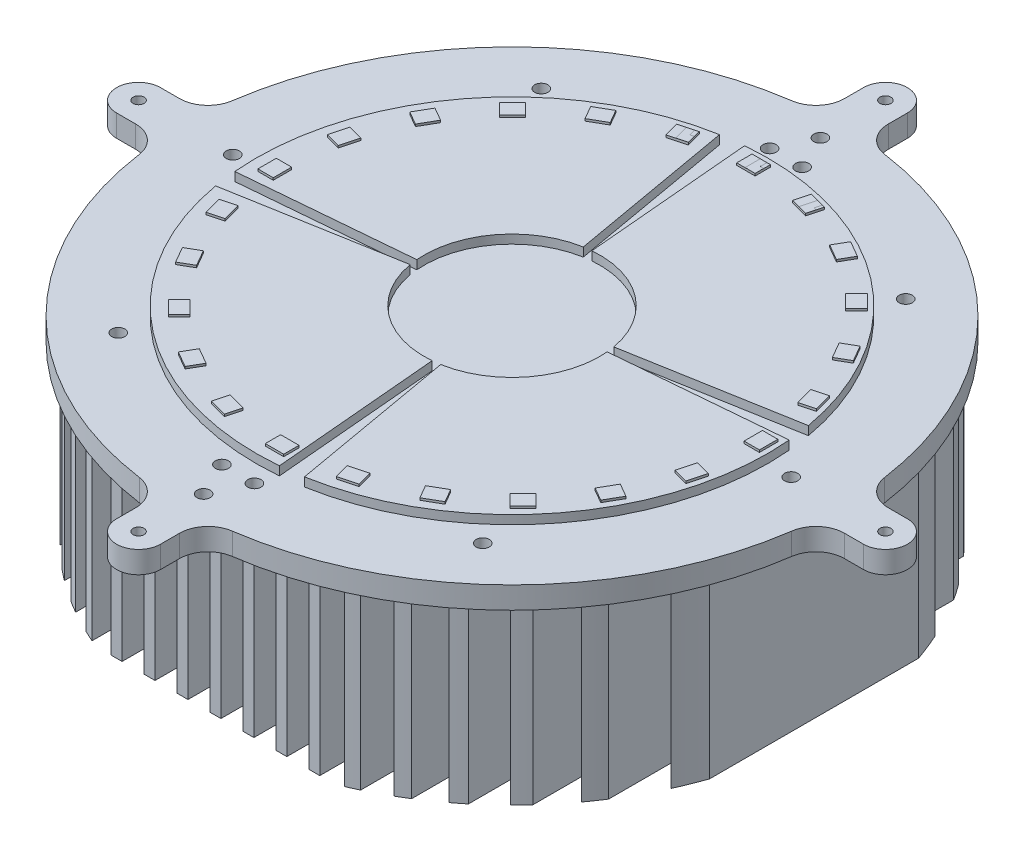
SolidWorks part; units mm, degrees
ref_plane "Front Plane" through (0, 0, 0) normal (0, 0, 1) x (1, 0, 0)
ref_plane "Top Plane" through (0, 0, 0) normal (0, 1, 0) x (1, 0, 0)
ref_plane "Right Plane" through (0, 0, 0) normal (1, 0, 0) x (0, 0, -1)
sketch "Sketch3" plane through (0, 0, 0) normal (0, 1, 0) x (1, 0, 0)
  line L0 (0, 0) -> (211.9111, 0) construction
  line L1 (0, 0) -> (-205.2426, 0) construction
  line L2 (0, 0) -> (0, 170) construction
  line L3 (0, 0) -> (0, -200) construction
  line L4 (161.3691, 10) -> (170, 10)
  line L5 (161.3691, -10) -> (170, -10)
  line L6 (-10, 161.3691) -> (-10, 170)
  line L7 (10, 161.3691) -> (10, 170)
  line L8 (10, -161.3691) -> (10, -170)
  line L9 (-10, -161.3691) -> (-10, -170)
  line L10 (-161.3691, -10) -> (-170, -10)
  line L11 (-161.3691, 10) -> (-170, 10)
  arc A0 (-21.1656, 148.4992) -> (-148.4992, 21.1656) centre (0, 0) ccw
  circle A1 centre (0, 170) radius 2.5
  arc A2 (-10, 170) -> (10, 170) centre (0, 170) cw
  arc A3 (10, 161.3691) -> (21.1656, 148.4992) centre (23, 161.3691) ccw
  arc A4 (-10, 161.3691) -> (-21.1656, 148.4992) centre (-23, 161.3691) cw
  arc A5 (170, 10) -> (170, -10) centre (170, 0) cw
  arc A6 (161.3691, 10) -> (148.4992, 21.1656) centre (161.3691, 23) cw
  circle A7 centre (170, 0) radius 2.5
  arc A8 (161.3691, -10) -> (148.4992, -21.1656) centre (161.3691, -23) ccw
  arc A9 (10, -170) -> (-10, -170) centre (0, -170) cw
  arc A10 (10, -161.3691) -> (21.1656, -148.4992) centre (23, -161.3691) cw
  circle A11 centre (0, -170) radius 2.5
  arc A12 (-10, -161.3691) -> (-21.1656, -148.4992) centre (-23, -161.3691) ccw
  arc A13 (-170, -10) -> (-170, 10) centre (-170, 0) cw
  arc A14 (-161.3691, -10) -> (-148.4992, -21.1656) centre (-161.3691, -23) cw
  circle A15 centre (-170, 0) radius 2.5
  arc A16 (-161.3691, 10) -> (-148.4992, 21.1656) centre (-161.3691, 23) ccw
  arc A17 (-148.4992, -21.1656) -> (-21.1656, -148.4992) centre (0, 0) ccw
  arc A18 (148.4992, 21.1656) -> (21.1656, 148.4992) centre (0, 0) ccw
  arc A19 (21.1656, -148.4992) -> (148.4992, -21.1656) centre (0, 0) ccw
  point P53 (0, 0)
  dimension "D1" = 300
  dimension "D4" = 5
  dimension "D2" = 4
extrude "Boss-Extrude4" add sketch "Sketch3" against normal blind 10
sketch "Sketch4" plane through (0, -10, 0) normal (0, -1, 0) x (1, 0, 0)
  line L0 (0, 0) -> (0, -192.7937) construction
  line L1 (0, 0) -> (0, 216.5128) construction
  line L2 (0, 0) -> (-235.9747, 0) construction
  line L3 (0, 0) -> (242.3846, 0) construction
  line L4 (2.5, -135) -> (-2.5, -135)
  line L5 (2.5, 135) -> (-2.5, 135)
  line L6 (-2.5, -135) -> (-2.5, 135)
  line L7 (2.5, -135) -> (2.5, 135)
  line L8 (12.5, -135) -> (12.5, 135)
  line L9 (17.5, -135) -> (12.5, -135)
  line L10 (17.5, -135) -> (17.5, 135)
  line L11 (17.5, 135) -> (12.5, 135)
  line L12 (27.5, -135) -> (27.5, 135)
  line L13 (32.5, -135) -> (27.5, -135)
  line L14 (32.5, -135) -> (32.5, 135)
  line L15 (32.5, 135) -> (27.5, 135)
  line L16 (42.5, -135) -> (42.5, 135)
  line L17 (47.5, -135) -> (42.5, -135)
  line L18 (47.5, -135) -> (47.5, 135)
  line L19 (47.5, 135) -> (42.5, 135)
  line L20 (57.5, -133.6563) -> (57.5, 133.6563)
  line L22 (62.5, -131.3925) -> (62.5, 131.3925)
  line L24 (72.5, -126.1507) -> (72.5, 126.1507)
  line L26 (77.5, -123.1422) -> (77.5, 123.1422)
  line L28 (87.5, -116.2497) -> (87.5, 116.2497)
  line L30 (92.5, -112.3121) -> (92.5, 112.3121)
  line L32 (102.5, -103.2666) -> (102.5, 103.2666)
  line L34 (107.5, -98.051) -> (107.5, 98.051)
  line L36 (117.5, -85.8138) -> (117.5, 85.8138)
  line L38 (122.5, -78.5111) -> (122.5, 78.5111)
  line L40 (132.5, -60.1166) -> (132.5, 60.1166)
  line L42 (137.5, -47.5815) -> (137.5, 47.5815)
  line L44 (-12.5, -135) -> (-17.5, -135)
  line L45 (-12.5, -135) -> (-12.5, 135)
  line L46 (-17.5, -135) -> (-17.5, 135)
  line L47 (-12.5, 135) -> (-17.5, 135)
  line L48 (-27.5, -135) -> (-32.5, -135)
  line L49 (-27.5, -135) -> (-27.5, 135)
  line L50 (-32.5, -135) -> (-32.5, 135)
  line L51 (-27.5, 135) -> (-32.5, 135)
  line L52 (-42.5, -135) -> (-47.5, -135)
  line L53 (-42.5, -135) -> (-42.5, 135)
  line L54 (-47.5, -135) -> (-47.5, 135)
  line L55 (-42.5, 135) -> (-47.5, 135)
  line L57 (-57.5, -133.6563) -> (-57.5, 133.6563)
  line L58 (-62.5, -131.3925) -> (-62.5, 131.3925)
  line L61 (-72.5, -126.1507) -> (-72.5, 126.1507)
  line L62 (-77.5, -123.1422) -> (-77.5, 123.1422)
  line L65 (-87.5, -116.2497) -> (-87.5, 116.2497)
  line L66 (-92.5, -112.3121) -> (-92.5, 112.3121)
  line L69 (-102.5, -103.2666) -> (-102.5, 103.2666)
  line L70 (-107.5, -98.051) -> (-107.5, 98.051)
  line L73 (-117.5, -85.8138) -> (-117.5, 85.8138)
  line L74 (-122.5, -78.5111) -> (-122.5, 78.5111)
  line L77 (-132.5, -60.1166) -> (-132.5, 60.1166)
  line L78 (-137.5, -47.5815) -> (-137.5, 47.5815)
  line L80 (2.5, -135) -> (-12.5, -135) construction
  line L81 (62.5, 135) -> (57.5, 135) [skipped]
  line L82 (77.5, 135) -> (72.5, 135) [skipped]
  line L83 (92.5, 135) -> (87.5, 135) [skipped]
  line L84 (107.5, 135) -> (102.5, 135) [skipped]
  line L85 (137.5, 135) -> (132.5, 135) [skipped]
  line L86 (122.5, 135) -> (117.5, 135) [skipped]
  line L87 (-57.5, 135) -> (-62.5, 135) [skipped]
  line L88 (-72.5, 135) -> (-77.5, 135) [skipped]
  line L89 (-87.5, 135) -> (-92.5, 135) [skipped]
  line L90 (-102.5, 135) -> (-107.5, 135) [skipped]
  line L91 (-117.5, 135) -> (-122.5, 135) [skipped]
  line L92 (-132.5, 135) -> (-137.5, 135) [skipped]
  line L93 (-57.5, -135) -> (-62.5, -135) [skipped]
  line L94 (62.5, -135) -> (57.5, -135) [skipped]
  line L95 (77.5, -135) -> (72.5, -135) [skipped]
  line L96 (137.5, -135) -> (132.5, -135) [skipped]
  line L97 (122.5, -135) -> (117.5, -135) [skipped]
  line L98 (107.5, -135) -> (102.5, -135) [skipped]
  line L99 (92.5, -135) -> (87.5, -135) [skipped]
  line L100 (-132.5, -135) -> (-137.5, -135) [skipped]
  line L101 (-117.5, -135) -> (-122.5, -135) [skipped]
  line L102 (-102.5, -135) -> (-107.5, -135) [skipped]
  line L103 (-87.5, -135) -> (-92.5, -135) [skipped]
  line L104 (-72.5, -135) -> (-77.5, -135) [skipped]
  arc A2 (132.5, -60.1166) -> (137.5, -47.5815) centre (0, 0) ccw
  arc A3 (117.5, -85.8138) -> (122.5, -78.5111) centre (0, 0) ccw
  arc A4 (102.5, -103.2666) -> (107.5, -98.051) centre (0, 0) ccw
  arc A5 (87.5, -116.2497) -> (92.5, -112.3121) centre (0, 0) ccw
  arc A6 (72.5, -126.1507) -> (77.5, -123.1422) centre (0, 0) ccw
  arc A7 (57.5, -133.6563) -> (62.5, -131.3925) centre (0, 0) ccw
  arc A8 (-77.5, -123.1422) -> (-72.5, -126.1507) centre (0, 0) ccw
  arc A9 (-62.5, -131.3925) -> (-57.5, -133.6563) centre (0, 0) ccw
  arc A10 (-92.5, -112.3121) -> (-87.5, -116.2497) centre (0, 0) ccw
  arc A11 (-107.5, -98.051) -> (-102.5, -103.2666) centre (0, 0) ccw
  arc A12 (-122.5, -78.5111) -> (-117.5, -85.8138) centre (0, 0) ccw
  arc A13 (-137.5, -47.5815) -> (-132.5, -60.1166) centre (0, 0) ccw
  arc A14 (137.5, 47.5815) -> (132.5, 60.1166) centre (0, 0) ccw
  arc A15 (122.5, 78.5111) -> (117.5, 85.8138) centre (0, 0) ccw
  arc A16 (107.5, 98.051) -> (102.5, 103.2666) centre (0, 0) ccw
  arc A17 (92.5, 112.3121) -> (87.5, 116.2497) centre (0, 0) ccw
  arc A18 (77.5, 123.1422) -> (72.5, 126.1507) centre (0, 0) ccw
  arc A19 (62.5, 131.3925) -> (57.5, 133.6563) centre (0, 0) ccw
  arc A20 (-57.5, 133.6563) -> (-62.5, 131.3925) centre (0, 0) ccw
  arc A21 (-72.5, 126.1507) -> (-77.5, 123.1422) centre (0, 0) ccw
  arc A22 (-87.5, 116.2497) -> (-92.5, 112.3121) centre (0, 0) ccw
  arc A23 (-102.5, 103.2666) -> (-107.5, 98.051) centre (0, 0) ccw
  arc A24 (-117.5, 85.8138) -> (-122.5, 78.5111) centre (0, 0) ccw
  arc A25 (-132.5, 60.1166) -> (-137.5, 47.5815) centre (0, 0) ccw
  dimension "D5" = 291
  dimension "D1" = 135
  dimension "D2" = 2.5
  dimension "D4" = 15
  dimension "D3" = 10
extrude "Boss-Extrude5" add sketch "Sketch4" along normal blind 80
sketch "Sketch8" plane through (0, 0, 0) normal (0, 1, 0) x (1, 0, 0)
  line L8 (3.4862, -39.8478) -> (10.1512, -116.0289)
  line L10 (-39.8478, -3.4862) -> (-116.0289, -10.1512)
  line L12 (-3.4862, 39.8478) -> (-10.1512, 116.0289)
  line L14 (39.8478, 3.4862) -> (116.0289, 10.1512)
  line L16 (6.9459, -39.3923) -> (20.2252, -114.7026)
  line L18 (39.3923, 6.9459) -> (114.7026, 20.2252)
  line L20 (-6.9459, 39.3923) -> (-20.2252, 114.7026)
  line L22 (-39.3923, -6.9459) -> (-114.7026, -20.2252)
  line L24 (30.6324, -25.7037) -> (89.1956, -74.844) [skipped]
  line L25 (25.7037, 30.6324) -> (74.844, 89.1956) [skipped]
  line L26 (-30.6324, 25.7037) -> (-89.1956, 74.844) [skipped]
  line L27 (-25.7037, -30.6324) -> (-74.844, -89.1956) [skipped]
  arc A0 (114.7026, 20.2252) -> (-10.1512, 116.0289) centre (0, 0) ccw
  arc A1 (-39.3923, -6.9459) -> (3.4862, -39.8478) centre (0, 0) ccw
  arc A2 (6.9459, -39.3923) -> (39.8478, 3.4862) centre (0, 0) ccw
  arc A3 (39.3923, 6.9459) -> (-3.4862, 39.8478) centre (0, 0) ccw
  arc A9 (-6.9459, 39.3923) -> (-39.8478, -3.4862) centre (0, 0) ccw
  arc A10 (-114.7026, -20.2252) -> (10.1512, -116.0289) centre (0, 0) ccw
  arc A11 (-20.2252, 114.7026) -> (-116.0289, -10.1512) centre (0, 0) ccw
  arc A12 (20.2252, -114.7026) -> (116.0289, 10.1512) centre (0, 0) ccw
  point P15 (0, 0)
  point P22 (0, 0)
  dimension "D2" = 8
extrude "Boss-Extrude7" add sketch "Sketch8" along normal blind 4
sketch "Sketch5" plane through (0, 4, 0) normal (0, 1, 0) x (1, 0, 0)
  line L0 (0, 0) -> (233.0388, 0) construction
  line L1 (0, 0) -> (-266.1331, 0) construction
  line L2 (0, 0) -> (0, 192.8201) construction
  line L3 (0, 0) -> (0, -200.634) construction
  line L4 (0, 113.4586) -> (4.19, 113.4586)
  line L5 (0, 113.4586) -> (-4.19, 113.4586)
  line L6 (4.19, 106.4786) -> (4.19, 113.4586)
  line L7 (-4.19, 106.4786) -> (-4.19, 113.4586)
  line L8 (0, 106.4786) -> (4.19, 106.4786)
  line L9 (0, 106.4786) -> (-4.19, 106.4786)
  line L10 (23.3125, 104.4034) -> (25.119, 111.1456)
  line L11 (29.1663, 110.0611) -> (25.119, 111.1456)
  line L12 (29.1663, 110.0611) -> (33.2135, 108.9767)
  line L13 (31.4069, 102.2345) -> (33.2135, 108.9767)
  line L14 (27.3597, 103.319) -> (31.4069, 102.2345)
  line L15 (27.3597, 103.319) -> (23.3125, 104.4034)
  line L16 (49.3407, 95.2808) -> (52.8307, 101.3256)
  line L17 (56.4594, 99.2306) -> (52.8307, 101.3256)
  line L18 (56.4594, 99.2306) -> (60.088, 97.1356)
  line L19 (56.598, 91.0908) -> (60.088, 97.1356)
  line L20 (52.9694, 93.1858) -> (56.598, 91.0908)
  line L21 (52.9694, 93.1858) -> (49.3407, 95.2808)
  line L22 (72.121, 79.7324) -> (77.0566, 84.668)
  line L23 (80.0194, 81.7052) -> (77.0566, 84.668)
  line L24 (80.0194, 81.7052) -> (82.9821, 78.7425)
  line L25 (78.0465, 73.8068) -> (82.9821, 78.7425)
  line L26 (75.0837, 76.7696) -> (78.0465, 73.8068)
  line L27 (75.0837, 76.7696) -> (72.121, 79.7324)
  line L28 (90.1008, 58.8179) -> (96.1456, 62.3079)
  line L29 (98.2406, 58.6792) -> (96.1456, 62.3079)
  line L30 (98.2406, 58.6792) -> (100.3356, 55.0506)
  line L31 (94.2908, 51.5606) -> (100.3356, 55.0506)
  line L32 (92.1958, 55.1892) -> (94.2908, 51.5606)
  line L33 (92.1958, 55.1892) -> (90.1008, 58.8179)
  line L34 (102.0549, 33.9624) -> (108.797, 35.769)
  line L35 (109.8815, 31.7218) -> (108.797, 35.769)
  line L36 (109.8815, 31.7218) -> (110.9659, 27.6745)
  line L37 (104.2238, 25.868) -> (110.9659, 27.6745)
  line L38 (103.1393, 29.9152) -> (104.2238, 25.868)
  line L39 (103.1393, 29.9152) -> (102.0549, 33.9624)
  line L40 (107.1686, 6.86) -> (114.1486, 6.86)
  line L41 (114.1486, 2.67) -> (114.1486, 6.86)
  line L42 (114.1486, 2.67) -> (114.1486, -1.52)
  line L43 (107.1686, -1.52) -> (114.1486, -1.52)
  line L44 (107.1686, 2.67) -> (107.1686, -1.52)
  line L45 (107.1686, 2.67) -> (107.1686, 6.86)
  line L46 (105.0934, -20.6425) -> (111.8356, -22.449)
  line L47 (110.7511, -26.4963) -> (111.8356, -22.449)
  line L48 (110.7511, -26.4963) -> (109.6667, -30.5435)
  line L49 (102.9245, -28.7369) -> (109.6667, -30.5435)
  line L50 (104.009, -24.6897) -> (102.9245, -28.7369)
  line L51 (104.009, -24.6897) -> (105.0934, -20.6425)
  line L52 (95.9708, -46.6707) -> (102.0156, -50.1607)
  line L53 (99.9206, -53.7894) -> (102.0156, -50.1607)
  line L54 (99.9206, -53.7894) -> (97.8256, -57.418)
  line L55 (91.7808, -53.928) -> (97.8256, -57.418)
  line L56 (93.8758, -50.2994) -> (91.7808, -53.928)
  line L57 (93.8758, -50.2994) -> (95.9708, -46.6707)
  line L58 (80.4224, -69.451) -> (85.358, -74.3866)
  line L59 (82.3952, -77.3494) -> (85.358, -74.3866)
  line L60 (82.3952, -77.3494) -> (79.4325, -80.3121)
  line L61 (74.4968, -75.3765) -> (79.4325, -80.3121)
  line L62 (77.4596, -72.4137) -> (74.4968, -75.3765)
  line L63 (77.4596, -72.4137) -> (80.4224, -69.451)
  line L64 (59.5079, -87.4308) -> (62.9979, -93.4756)
  line L65 (59.3692, -95.5706) -> (62.9979, -93.4756)
  line L66 (59.3692, -95.5706) -> (55.7406, -97.6656)
  line L67 (52.2506, -91.6208) -> (55.7406, -97.6656)
  line L68 (55.8792, -89.5258) -> (52.2506, -91.6208)
  line L69 (55.8792, -89.5258) -> (59.5079, -87.4308)
  line L70 (34.6524, -99.3849) -> (36.459, -106.127)
  line L71 (32.4118, -107.2115) -> (36.459, -106.127)
  line L72 (32.4118, -107.2115) -> (28.3645, -108.2959)
  line L73 (26.558, -101.5538) -> (28.3645, -108.2959)
  line L74 (30.6052, -100.4693) -> (26.558, -101.5538)
  line L75 (30.6052, -100.4693) -> (34.6524, -99.3849)
  line L76 (7.55, -104.4986) -> (7.55, -111.4786)
  line L77 (3.36, -111.4786) -> (7.55, -111.4786)
  line L78 (3.36, -111.4786) -> (-0.83, -111.4786)
  line L79 (-0.83, -104.4986) -> (-0.83, -111.4786)
  line L80 (3.36, -104.4986) -> (-0.83, -104.4986)
  line L81 (3.36, -104.4986) -> (7.55, -104.4986)
  line L82 (-19.9525, -102.4234) -> (-21.759, -109.1656)
  line L83 (-25.8063, -108.0811) -> (-21.759, -109.1656)
  line L84 (-25.8063, -108.0811) -> (-29.8535, -106.9967)
  line L85 (-28.0469, -100.2545) -> (-29.8535, -106.9967)
  line L86 (-23.9997, -101.339) -> (-28.0469, -100.2545)
  line L87 (-23.9997, -101.339) -> (-19.9525, -102.4234)
  line L88 (-45.9807, -93.3008) -> (-49.4707, -99.3456)
  line L89 (-53.0994, -97.2506) -> (-49.4707, -99.3456)
  line L90 (-53.0994, -97.2506) -> (-56.728, -95.1556)
  line L91 (-53.238, -89.1108) -> (-56.728, -95.1556)
  line L92 (-49.6094, -91.2058) -> (-53.238, -89.1108)
  line L93 (-49.6094, -91.2058) -> (-45.9807, -93.3008)
  line L94 (-68.761, -77.7524) -> (-73.6966, -82.688)
  line L95 (-76.6594, -79.7252) -> (-73.6966, -82.688)
  line L96 (-76.6594, -79.7252) -> (-79.6221, -76.7625)
  line L97 (-74.6865, -71.8268) -> (-79.6221, -76.7625)
  line L98 (-71.7237, -74.7896) -> (-74.6865, -71.8268)
  line L99 (-71.7237, -74.7896) -> (-68.761, -77.7524)
  line L100 (-86.7408, -56.8379) -> (-92.7856, -60.3279)
  line L101 (-94.8806, -56.6992) -> (-92.7856, -60.3279)
  line L102 (-94.8806, -56.6992) -> (-96.9756, -53.0706)
  line L103 (-90.9308, -49.5806) -> (-96.9756, -53.0706)
  line L104 (-88.8358, -53.2092) -> (-90.9308, -49.5806)
  line L105 (-88.8358, -53.2092) -> (-86.7408, -56.8379)
  line L106 (-98.6949, -31.9824) -> (-105.437, -33.789)
  line L107 (-106.5215, -29.7418) -> (-105.437, -33.789)
  line L108 (-106.5215, -29.7418) -> (-107.6059, -25.6945)
  line L109 (-100.8638, -23.888) -> (-107.6059, -25.6945)
  line L110 (-99.7793, -27.9352) -> (-100.8638, -23.888)
  line L111 (-99.7793, -27.9352) -> (-98.6949, -31.9824)
  line L112 (-103.8086, -4.88) -> (-110.7886, -4.88)
  line L113 (-110.7886, -0.69) -> (-110.7886, -4.88)
  line L114 (-110.7886, -0.69) -> (-110.7886, 3.5)
  line L115 (-103.8086, 3.5) -> (-110.7886, 3.5)
  line L116 (-103.8086, -0.69) -> (-103.8086, 3.5)
  line L117 (-103.8086, -0.69) -> (-103.8086, -4.88)
  line L118 (-101.7334, 22.6225) -> (-108.4756, 24.429)
  line L119 (-107.3911, 28.4763) -> (-108.4756, 24.429)
  line L120 (-107.3911, 28.4763) -> (-106.3067, 32.5235)
  line L121 (-99.5645, 30.7169) -> (-106.3067, 32.5235)
  line L122 (-100.649, 26.6697) -> (-99.5645, 30.7169)
  line L123 (-100.649, 26.6697) -> (-101.7334, 22.6225)
  line L124 (-92.6108, 48.6507) -> (-98.6556, 52.1407)
  line L125 (-96.5606, 55.7694) -> (-98.6556, 52.1407)
  line L126 (-96.5606, 55.7694) -> (-94.4656, 59.398)
  line L127 (-88.4208, 55.908) -> (-94.4656, 59.398)
  line L128 (-90.5158, 52.2794) -> (-88.4208, 55.908)
  line L129 (-90.5158, 52.2794) -> (-92.6108, 48.6507)
  line L130 (-77.0624, 71.431) -> (-81.998, 76.3666)
  line L131 (-79.0352, 79.3294) -> (-81.998, 76.3666)
  line L132 (-79.0352, 79.3294) -> (-76.0725, 82.2921)
  line L133 (-71.1368, 77.3565) -> (-76.0725, 82.2921)
  line L134 (-74.0996, 74.3937) -> (-71.1368, 77.3565)
  line L135 (-74.0996, 74.3937) -> (-77.0624, 71.431)
  line L136 (-56.1479, 89.4108) -> (-59.6379, 95.4556)
  line L137 (-56.0092, 97.5506) -> (-59.6379, 95.4556)
  line L138 (-56.0092, 97.5506) -> (-52.3806, 99.6456)
  line L139 (-48.8906, 93.6008) -> (-52.3806, 99.6456)
  line L140 (-52.5192, 91.5058) -> (-48.8906, 93.6008)
  line L141 (-52.5192, 91.5058) -> (-56.1479, 89.4108)
  line L142 (-31.2924, 101.3649) -> (-33.099, 108.107)
  line L143 (-29.0518, 109.1915) -> (-33.099, 108.107)
  line L144 (-29.0518, 109.1915) -> (-25.0045, 110.2759)
  line L145 (-23.198, 103.5338) -> (-25.0045, 110.2759)
  line L146 (-27.2452, 102.4493) -> (-23.198, 103.5338)
  line L147 (-27.2452, 102.4493) -> (-31.2924, 101.3649)
  point P33 (1.68, 0.99)
  dimension "D1" = 4.19
  dimension "D2" = 6.98
  dimension "D4" = 4.19
  dimension "D3" = 24
extrude "Boss-Extrude6" add sketch "Sketch5" along normal blind 1
sketch "Sketch7" plane through (0, 0, 0) normal (0, 1, 0) x (1, 0, 0)
  line L0 (0, 0) -> (0, 199.2983) construction
  line L1 (180, 0) -> (-209.1437, 0) construction
  line L2 (0, 0) -> (0, -219.846) construction
  arc A0 (170, -10) -> (170, 10) centre (170, 0) ccw construction
  circle A1 centre (-127.0882, 0) radius 3
  circle A2 centre (0, 140.3779) radius 3
  circle A3 centre (0, -140.3779) radius 3
  circle A4 centre (127.0882, 0) radius 3
  circle A5 centre (-67.7124, 0) radius 3
  circle A6 centre (-52.1309, 49.6625) radius 3
  circle A7 centre (52.1309, 49.6625) radius 3
  circle A8 centre (52.1309, -49.6625) radius 3
  circle A9 centre (-52.1309, -49.6625) radius 3
  circle A10 centre (67.7124, 0) radius 3
  circle A11 centre (-82.9543, 96.2809) radius 3
  circle A12 centre (82.9543, 96.2809) radius 3
  circle A13 centre (82.9543, -96.2809) radius 3
  circle A14 centre (-82.9543, -96.2809) radius 3
  circle A15 centre (7.3999, -124.6624) radius 3
  circle A16 centre (-7.3999, -124.6624) radius 3
  circle A17 centre (7.3999, 124.6624) radius 3
  circle A18 centre (-7.3999, 124.6624) radius 3
  dimension "D2" = 6
extrude "Cut-Extrude1" cut sketch "Sketch7" against normal blind 10
sketch "Sketch10" plane through (0, 5, 0) normal (0, 1, 0) x (1, 0, 0)
  line L0 (-4.19, 113.4586) -> (-4.19, 106.4786)
  line L1 (-4.19, 106.4786) -> (4.19, 106.4786)
  line L2 (4.19, 106.4786) -> (4.19, 113.4586)
  line L3 (4.19, 113.4586) -> (-4.19, 113.4586)
  line L4 (0, 113.4586) -> (0.0001, 113.4586)
  line L5 (2.625, 113.3936) -> (2.625, 110.3936)
  line L6 (4.125, 110.3936) -> (4.125, 106.5436)
  line L7 (4.125, 106.5436) -> (-0.425, 106.5436)
  line L8 (0, 0) -> (0, 207.6989) construction
  line L9 (0, 0) -> (0, -235.1351) construction
  line L10 (2.625, 110.3936) -> (4.125, 110.3936)
  line L11 (-0.425, 113.3936) -> (-0.425, 106.5436)
  line L12 (2.625, 113.3936) -> (-0.425, 113.3936)
  line L13 (0, 0) -> (238.2914, 0) construction
  line L14 (0, 0) -> (-206.0878, 0) construction
  line L15 (31.2113, 106.34) -> (32.3574, 106.0329)
  line L16 (32.3574, 106.0329) -> (31.361, 102.3141)
  line L17 (31.361, 102.3141) -> (27.2688, 103.4106)
  line L18 (29.0417, 110.0272) -> (27.2688, 103.4106)
  line L19 (31.9878, 109.2378) -> (29.0417, 110.0272)
  line L20 (31.9878, 109.2378) -> (31.2113, 106.34)
  line L21 (57.4701, 94.2911) -> (58.7691, 93.5411)
  line L22 (58.7691, 93.5411) -> (56.8441, 90.2069)
  line L23 (56.8441, 90.2069) -> (52.9037, 92.4819)
  line L24 (56.3287, 98.4142) -> (52.9037, 92.4819)
  line L25 (58.9701, 96.8892) -> (56.3287, 98.4142)
  line L26 (58.9701, 96.8892) -> (57.4701, 94.2911)
  line L27 (79.9162, 76.2039) -> (80.9769, 75.1432)
  line L28 (80.9769, 75.1432) -> (78.2545, 72.4209)
  line L29 (78.2545, 72.4209) -> (75.0372, 75.6382)
  line L30 (79.8808, 80.4819) -> (75.0372, 75.6382)
  line L31 (82.0375, 78.3252) -> (79.8808, 80.4819)
  line L32 (82.0375, 78.3252) -> (79.9162, 76.2039)
  line L33 (96.9161, 52.9235) -> (97.6661, 51.6244)
  line L34 (97.6661, 51.6244) -> (94.3319, 49.6994)
  line L35 (94.3319, 49.6994) -> (92.0569, 53.6398)
  line L36 (97.9892, 57.0648) -> (92.0569, 53.6398)
  line L37 (99.5142, 54.4235) -> (97.9892, 57.0648)
  line L38 (99.5142, 54.4235) -> (96.9161, 52.9235)
  line L39 (107.3114, 26.0364) -> (107.6996, 24.5875)
  line L40 (107.6996, 24.5875) -> (103.9808, 23.5911)
  line L41 (103.9808, 23.5911) -> (102.8032, 27.986)
  line L42 (109.4198, 29.7589) -> (102.8032, 27.986)
  line L43 (110.2092, 26.8129) -> (109.4198, 29.7589)
  line L44 (110.2092, 26.8129) -> (107.3114, 26.0364)
  line L45 (110.3936, -2.625) -> (110.3936, -4.125)
  line L46 (110.3936, -4.125) -> (106.5436, -4.125)
  line L47 (106.5436, -4.125) -> (106.5436, 0.425)
  line L48 (113.3936, 0.425) -> (106.5436, 0.425)
  line L49 (113.3936, -2.625) -> (113.3936, 0.425)
  line L50 (113.3936, -2.625) -> (110.3936, -2.625)
  line L51 (105.9526, -31.1075) -> (105.5644, -32.5564)
  line L52 (105.5644, -32.5564) -> (101.8456, -31.5599)
  line L53 (101.8456, -31.5599) -> (103.0232, -27.165)
  line L54 (109.6398, -28.9379) -> (103.0232, -27.165)
  line L55 (108.8504, -31.884) -> (109.6398, -28.9379)
  line L56 (108.8504, -31.884) -> (105.9526, -31.1075)
  line L57 (94.2911, -57.4701) -> (93.5411, -58.7691)
  line L58 (93.5411, -58.7691) -> (90.2069, -56.8441)
  line L59 (90.2069, -56.8441) -> (92.4819, -52.9037)
  line L60 (98.4142, -56.3287) -> (92.4819, -52.9037)
  line L61 (96.8892, -58.9701) -> (98.4142, -56.3287)
  line L62 (96.8892, -58.9701) -> (94.2911, -57.4701)
  line L63 (76.2039, -79.9162) -> (75.1432, -80.9769)
  line L64 (75.1432, -80.9769) -> (72.4209, -78.2545)
  line L65 (72.4209, -78.2545) -> (75.6382, -75.0372)
  line L66 (80.4819, -79.8808) -> (75.6382, -75.0372)
  line L67 (78.3252, -82.0375) -> (80.4819, -79.8808)
  line L68 (78.3252, -82.0375) -> (76.2039, -79.9162)
  line L69 (52.9235, -96.9161) -> (51.6244, -97.6661)
  line L70 (51.6244, -97.6661) -> (49.6994, -94.3319)
  line L71 (49.6994, -94.3319) -> (53.6398, -92.0569)
  line L72 (57.0648, -97.9892) -> (53.6398, -92.0569)
  line L73 (54.4235, -99.5142) -> (57.0648, -97.9892)
  line L74 (54.4235, -99.5142) -> (52.9235, -96.9161)
  line L75 (26.0364, -107.3114) -> (24.5875, -107.6996)
  line L76 (24.5875, -107.6996) -> (23.5911, -103.9808)
  line L77 (23.5911, -103.9808) -> (27.986, -102.8032)
  line L78 (29.7589, -109.4198) -> (27.986, -102.8032)
  line L79 (26.8129, -110.2092) -> (29.7589, -109.4198)
  line L80 (26.8129, -110.2092) -> (26.0364, -107.3114)
  line L81 (-2.625, -110.3936) -> (-4.125, -110.3936)
  line L82 (-4.125, -110.3936) -> (-4.125, -106.5436)
  line L83 (-4.125, -106.5436) -> (0.425, -106.5436)
  line L84 (0.425, -113.3936) -> (0.425, -106.5436)
  line L85 (-2.625, -113.3936) -> (0.425, -113.3936)
  line L86 (-2.625, -113.3936) -> (-2.625, -110.3936)
  line L87 (-31.1075, -105.9526) -> (-32.5564, -105.5644)
  line L88 (-32.5564, -105.5644) -> (-31.5599, -101.8456)
  line L89 (-31.5599, -101.8456) -> (-27.165, -103.0232)
  line L90 (-28.9379, -109.6398) -> (-27.165, -103.0232)
  line L91 (-31.884, -108.8504) -> (-28.9379, -109.6398)
  line L92 (-31.884, -108.8504) -> (-31.1075, -105.9526)
  line L93 (-57.4701, -94.2911) -> (-58.7691, -93.5411)
  line L94 (-58.7691, -93.5411) -> (-56.8441, -90.2069)
  line L95 (-56.8441, -90.2069) -> (-52.9037, -92.4819)
  line L96 (-56.3287, -98.4142) -> (-52.9037, -92.4819)
  line L97 (-58.9701, -96.8892) -> (-56.3287, -98.4142)
  line L98 (-58.9701, -96.8892) -> (-57.4701, -94.2911)
  line L99 (-79.9162, -76.2039) -> (-80.9769, -75.1432)
  line L100 (-80.9769, -75.1432) -> (-78.2545, -72.4209)
  line L101 (-78.2545, -72.4209) -> (-75.0372, -75.6382)
  line L102 (-79.8808, -80.4819) -> (-75.0372, -75.6382)
  line L103 (-82.0375, -78.3252) -> (-79.8808, -80.4819)
  line L104 (-82.0375, -78.3252) -> (-79.9162, -76.2039)
  line L105 (-96.9161, -52.9235) -> (-97.6661, -51.6244)
  line L106 (-97.6661, -51.6244) -> (-94.3319, -49.6994)
  line L107 (-94.3319, -49.6994) -> (-92.0569, -53.6398)
  line L108 (-97.9892, -57.0648) -> (-92.0569, -53.6398)
  line L109 (-99.5142, -54.4235) -> (-97.9892, -57.0648)
  line L110 (-99.5142, -54.4235) -> (-96.9161, -52.9235)
  line L111 (-107.3114, -26.0364) -> (-107.6996, -24.5875)
  line L112 (-107.6996, -24.5875) -> (-103.9808, -23.5911)
  line L113 (-103.9808, -23.5911) -> (-102.8032, -27.986)
  line L114 (-109.4198, -29.7589) -> (-102.8032, -27.986)
  line L115 (-110.2092, -26.8129) -> (-109.4198, -29.7589)
  line L116 (-110.2092, -26.8129) -> (-107.3114, -26.0364)
  line L117 (-110.3936, 2.625) -> (-110.3936, 4.125)
  line L118 (-110.3936, 4.125) -> (-106.5436, 4.125)
  line L119 (-106.5436, 4.125) -> (-106.5436, -0.425)
  line L120 (-113.3936, -0.425) -> (-106.5436, -0.425)
  line L121 (-113.3936, 2.625) -> (-113.3936, -0.425)
  line L122 (-113.3936, 2.625) -> (-110.3936, 2.625)
  line L123 (-105.9526, 31.1075) -> (-105.5644, 32.5564)
  line L124 (-105.5644, 32.5564) -> (-101.8456, 31.5599)
  line L125 (-101.8456, 31.5599) -> (-103.0232, 27.165)
  line L126 (-109.6398, 28.9379) -> (-103.0232, 27.165)
  line L127 (-108.8504, 31.884) -> (-109.6398, 28.9379)
  line L128 (-108.8504, 31.884) -> (-105.9526, 31.1075)
  line L129 (-94.2911, 57.4701) -> (-93.5411, 58.7691)
  line L130 (-93.5411, 58.7691) -> (-90.2069, 56.8441)
  line L131 (-90.2069, 56.8441) -> (-92.4819, 52.9037)
  line L132 (-98.4142, 56.3287) -> (-92.4819, 52.9037)
  line L133 (-96.8892, 58.9701) -> (-98.4142, 56.3287)
  line L134 (-96.8892, 58.9701) -> (-94.2911, 57.4701)
  line L135 (-76.2039, 79.9162) -> (-75.1432, 80.9769)
  line L136 (-75.1432, 80.9769) -> (-72.4209, 78.2545)
  line L137 (-72.4209, 78.2545) -> (-75.6382, 75.0372)
  line L138 (-80.4819, 79.8808) -> (-75.6382, 75.0372)
  line L139 (-78.3252, 82.0375) -> (-80.4819, 79.8808)
  line L140 (-78.3252, 82.0375) -> (-76.2039, 79.9162)
  line L141 (-52.9235, 96.9161) -> (-51.6244, 97.6661)
  line L142 (-51.6244, 97.6661) -> (-49.6994, 94.3319)
  line L143 (-49.6994, 94.3319) -> (-53.6398, 92.0569)
  line L144 (-57.0648, 97.9892) -> (-53.6398, 92.0569)
  line L145 (-54.4235, 99.5142) -> (-57.0648, 97.9892)
  line L146 (-54.4235, 99.5142) -> (-52.9235, 96.9161)
  line L147 (-25.9151, 106.8588) -> (-24.274, 107.2985)
  line L148 (-24.274, 107.2985) -> (-23.2776, 103.5797)
  line L149 (-23.2776, 103.5797) -> (-27.8648, 102.3506)
  line L150 (-29.6377, 108.9672) -> (-27.8648, 102.3506)
  line L151 (-26.6916, 109.7566) -> (-29.6377, 108.9672)
  line L152 (-26.6916, 109.7566) -> (-25.9151, 106.8588)
  line L154 (-31.2924, 101.3649) -> (-23.198, 103.5338) construction
  line L155 (-23.198, 103.5338) -> (-25.0045, 110.2759) construction
  line L156 (23.3125, 104.4034) -> (31.4069, 102.2345) construction
  line L157 (31.4069, 102.2345) -> (33.2135, 108.9767) construction
  point P163 (0, 0)
  dimension "D1" = 0.065
  dimension "D2" = 0.065
  dimension "D3" = 0.065
  dimension "D4" = 0.065
extrude "Boss-Extrude8" add sketch "Sketch10" along normal blind 0.01 contours L10 L6 L7 L11 L12 L5 | L147 L148 L149 L150 L151 L152 | L15 L16 L17 L18 L19 L20
sketch "Sketch11" plane through (0, 5, 0) normal (0, 1, 0) x (1, 0, 0)
  line L1 (0, 0) -> (0, 191.6119) construction
  line L2 (-4.19, 113.4586) -> (9.0771, 113.4586) construction
  line L3 (-1.225, 104.4986) -> (4.19, 104.4986)
  line L4 (4.19, 113.4586) -> (4.19, 104.4986)
  line L5 (-1.225, 113.4586) -> (-1.225, 104.4986)
  line L6 (-1.225, 105.1386) -> (4.19, 105.1386)
  line L7 (-0.425, 113.3936) -> (-0.425, 106.5436) construction
  line L8 (-1.225, 113.4586) -> (4.19, 113.4586)
  line L9 (-1.225, 105.7786) -> (4.19, 105.7786)
  line L10 (-1.225, 106.4186) -> (4.19, 106.4186)
  line L11 (-1.225, 107.0586) -> (4.19, 107.0586)
  line L12 (-1.225, 107.6986) -> (4.19, 107.6986)
  line L13 (-1.225, 108.3386) -> (4.19, 108.3386)
  line L14 (-1.225, 108.9786) -> (4.19, 108.9786)
  line L15 (-1.225, 109.6186) -> (4.19, 109.6186)
  line L16 (-1.225, 110.2586) -> (4.19, 110.2586)
  line L17 (-1.225, 110.8986) -> (4.19, 110.8986)
  line L18 (-1.225, 111.5386) -> (4.19, 111.5386)
  line L19 (-1.225, 112.1786) -> (4.19, 112.1786)
  line L20 (-1.225, 112.8186) -> (4.19, 112.8186)
  line L21 (-0.585, 113.4681) -> (-0.585, 104.489)
  line L22 (0.055, 113.4681) -> (0.055, 104.489)
  line L23 (0.695, 113.4681) -> (0.695, 104.489)
  line L24 (1.335, 113.4681) -> (1.335, 104.489)
  line L25 (1.975, 113.4681) -> (1.975, 104.489)
  line L26 (2.615, 113.4681) -> (2.615, 104.489)
  line L27 (3.255, 113.4681) -> (3.255, 104.489)
  line L28 (3.895, 113.4681) -> (3.895, 104.489)
  line L29 (-1.225, 113.4586) -> (4.19, 113.4586)
  line L30 (4.535, 113.4586) -> (4.535, 104.4986)
  line L31 (-1.225, 113.4586) -> (-1.225, 112.8186) construction
  circle A0 centre (-1.225, 113.4586) radius 0.15
  circle A1 centre (-0.585, 113.4586) radius 0.15
  circle A2 centre (0.055, 113.4586) radius 0.15
  circle A3 centre (0.695, 113.4586) radius 0.15
  circle A4 centre (1.335, 113.4586) radius 0.15
  circle A5 centre (1.975, 113.4586) radius 0.15
  circle A6 centre (2.615, 113.4681) radius 0.1475
  circle A7 centre (3.255, 113.4586) radius 0.15
  circle A8 centre (3.895, 113.4681) radius 0.1475
  circle A9 centre (4.535, 113.4586) radius 0.15
  circle A10 centre (-1.225, 112.8186) radius 0.15
  circle A11 centre (-0.585, 112.8186) radius 0.15
  circle A12 centre (0.055, 112.8186) radius 0.15
  circle A13 centre (0.695, 112.8186) radius 0.15
  circle A14 centre (1.335, 112.8186) radius 0.15
  circle A15 centre (1.975, 112.8186) radius 0.15
  circle A16 centre (2.615, 112.8281) radius 0.1475
  circle A17 centre (3.255, 112.8186) radius 0.15
  circle A18 centre (3.895, 112.8281) radius 0.1475
  circle A19 centre (4.535, 112.8186) radius 0.15
  circle A20 centre (-1.225, 112.1786) radius 0.15
  circle A21 centre (-0.585, 112.1786) radius 0.15
  circle A22 centre (0.055, 112.1786) radius 0.15
  circle A23 centre (0.695, 112.1786) radius 0.15
  circle A24 centre (1.335, 112.1786) radius 0.15
  circle A25 centre (1.975, 112.1786) radius 0.15
  circle A26 centre (2.615, 112.1881) radius 0.1475
  circle A27 centre (3.255, 112.1786) radius 0.15
  circle A28 centre (3.895, 112.1881) radius 0.1475
  circle A29 centre (4.535, 112.1786) radius 0.15
  circle A30 centre (-1.225, 111.5386) radius 0.15
  circle A31 centre (-0.585, 111.5386) radius 0.15
  circle A32 centre (0.055, 111.5386) radius 0.15
  circle A33 centre (0.695, 111.5386) radius 0.15
  circle A34 centre (1.335, 111.5386) radius 0.15
  circle A35 centre (1.975, 111.5386) radius 0.15
  circle A36 centre (2.615, 111.5481) radius 0.1475
  circle A37 centre (3.255, 111.5386) radius 0.15
  circle A38 centre (3.895, 111.5481) radius 0.1475
  circle A39 centre (4.535, 111.5386) radius 0.15
  circle A40 centre (-1.225, 110.8986) radius 0.15
  circle A41 centre (-0.585, 110.8986) radius 0.15
  circle A42 centre (0.055, 110.8986) radius 0.15
  circle A43 centre (0.695, 110.8986) radius 0.15
  circle A44 centre (1.335, 110.8986) radius 0.15
  circle A45 centre (1.975, 110.8986) radius 0.15
  circle A46 centre (2.615, 110.9081) radius 0.1475
  circle A47 centre (3.255, 110.8986) radius 0.15
  circle A48 centre (3.895, 110.9081) radius 0.1475
  circle A49 centre (4.535, 110.8986) radius 0.15
  circle A50 centre (-1.225, 110.2586) radius 0.15
  circle A51 centre (-0.585, 110.2586) radius 0.15
  circle A52 centre (0.055, 110.2586) radius 0.15
  circle A53 centre (0.695, 110.2586) radius 0.15
  circle A54 centre (1.335, 110.2586) radius 0.15
  circle A55 centre (1.975, 110.2586) radius 0.15
  circle A56 centre (2.615, 110.2681) radius 0.1475
  circle A57 centre (3.255, 110.2586) radius 0.15
  circle A58 centre (3.895, 110.2681) radius 0.1475
  circle A59 centre (4.535, 110.2586) radius 0.15
  circle A60 centre (-1.225, 109.6186) radius 0.15
  circle A61 centre (-0.585, 109.6186) radius 0.15
  circle A62 centre (0.055, 109.6186) radius 0.15
  circle A63 centre (0.695, 109.6186) radius 0.15
  circle A64 centre (1.335, 109.6186) radius 0.15
  circle A65 centre (1.975, 109.6186) radius 0.15
  circle A66 centre (2.615, 109.6281) radius 0.1475
  circle A67 centre (3.255, 109.6186) radius 0.15
  circle A68 centre (3.895, 109.6281) radius 0.1475
  circle A69 centre (4.535, 109.6186) radius 0.15
  circle A70 centre (-1.225, 108.9786) radius 0.15
  circle A71 centre (-0.585, 108.9786) radius 0.15
  circle A72 centre (0.055, 108.9786) radius 0.15
  circle A73 centre (0.695, 108.9786) radius 0.15
  circle A74 centre (1.335, 108.9786) radius 0.15
  circle A75 centre (1.975, 108.9786) radius 0.15
  circle A76 centre (2.615, 108.9881) radius 0.1475
  circle A77 centre (3.255, 108.9786) radius 0.15
  circle A78 centre (3.895, 108.9881) radius 0.1475
  circle A79 centre (4.535, 108.9786) radius 0.15
  circle A80 centre (-1.225, 108.3386) radius 0.15
  circle A81 centre (-0.585, 108.3386) radius 0.15
  circle A82 centre (0.055, 108.3386) radius 0.15
  circle A83 centre (0.695, 108.3386) radius 0.15
  circle A84 centre (1.335, 108.3386) radius 0.15
  circle A85 centre (1.975, 108.3386) radius 0.15
  circle A86 centre (2.615, 108.3481) radius 0.1475
  circle A87 centre (3.255, 108.3386) radius 0.15
  circle A88 centre (3.895, 108.3481) radius 0.1475
  circle A89 centre (4.535, 108.3386) radius 0.15
  circle A90 centre (-1.225, 107.6986) radius 0.15
  circle A91 centre (-0.585, 107.6986) radius 0.15
  circle A92 centre (0.055, 107.6986) radius 0.15
  circle A93 centre (0.695, 107.6986) radius 0.15
  circle A94 centre (1.335, 107.6986) radius 0.15
  circle A95 centre (1.975, 107.6986) radius 0.15
  circle A96 centre (2.615, 107.7081) radius 0.1475
  circle A97 centre (3.255, 107.6986) radius 0.15
  circle A98 centre (3.895, 107.7081) radius 0.1475
  circle A99 centre (4.535, 107.6986) radius 0.15
  circle A100 centre (-1.225, 107.0586) radius 0.15
  circle A101 centre (-0.585, 107.0586) radius 0.15
  circle A102 centre (0.055, 107.0586) radius 0.15
  circle A103 centre (0.695, 107.0586) radius 0.15
  circle A104 centre (1.335, 107.0586) radius 0.15
  circle A105 centre (1.975, 107.0586) radius 0.15
  circle A106 centre (2.615, 107.0681) radius 0.1475
  circle A107 centre (3.255, 107.0586) radius 0.15
  circle A108 centre (3.895, 107.0681) radius 0.1475
  circle A109 centre (4.535, 107.0586) radius 0.15
  circle A110 centre (-1.225, 106.4186) radius 0.15
  circle A111 centre (-0.585, 106.4186) radius 0.15
  circle A112 centre (0.055, 106.4186) radius 0.15
  circle A113 centre (0.695, 106.4186) radius 0.15
  circle A114 centre (1.335, 106.4186) radius 0.15
  circle A115 centre (1.975, 106.4186) radius 0.15
  circle A116 centre (2.615, 106.4281) radius 0.1475
  circle A117 centre (3.255, 106.4186) radius 0.15
  circle A118 centre (3.895, 106.4281) radius 0.1475
  circle A119 centre (4.535, 106.4186) radius 0.15
  circle A120 centre (-1.225, 105.7786) radius 0.15
  circle A121 centre (-0.585, 105.7786) radius 0.15
  circle A122 centre (0.055, 105.7786) radius 0.15
  circle A123 centre (0.695, 105.7786) radius 0.15
  circle A124 centre (1.335, 105.7786) radius 0.15
  circle A125 centre (1.975, 105.7786) radius 0.15
  circle A126 centre (2.615, 105.7881) radius 0.1475
  circle A127 centre (3.255, 105.7786) radius 0.15
  circle A128 centre (3.895, 105.7881) radius 0.1475
  circle A129 centre (4.535, 105.7786) radius 0.15
  circle A130 centre (-1.225, 105.1386) radius 0.15
  circle A131 centre (-0.585, 105.1386) radius 0.15
  circle A132 centre (0.055, 105.1386) radius 0.15
  circle A133 centre (0.695, 105.1386) radius 0.15
  circle A134 centre (1.335, 105.1386) radius 0.15
  circle A135 centre (1.975, 105.1386) radius 0.15
  circle A136 centre (2.615, 105.1481) radius 0.1475
  circle A137 centre (3.255, 105.1386) radius 0.15
  circle A138 centre (3.895, 105.1481) radius 0.1475
  circle A139 centre (4.535, 105.1386) radius 0.15
  circle A140 centre (-1.225, 104.4986) radius 0.15
  circle A141 centre (-0.585, 104.4986) radius 0.15
  circle A142 centre (0.055, 104.4986) radius 0.15
  circle A143 centre (0.695, 104.4986) radius 0.15
  circle A144 centre (1.335, 104.4986) radius 0.15
  circle A145 centre (1.975, 104.4986) radius 0.15
  circle A146 centre (2.615, 104.5081) radius 0.1475
  circle A147 centre (3.255, 104.4986) radius 0.15
  circle A148 centre (3.895, 104.5081) radius 0.1475
  circle A149 centre (4.535, 104.4986) radius 0.15
  dimension "D4" = 0.64
  dimension "D1" = 10
  dimension "D2" = 0.8
  dimension "D3" = 15
